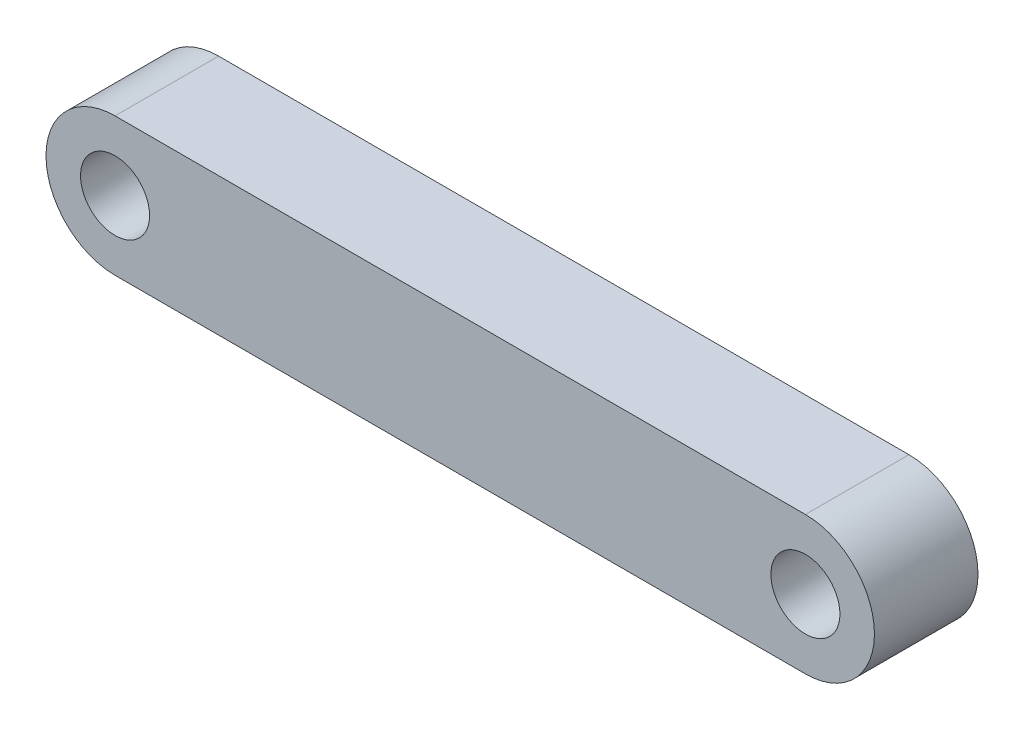
SolidWorks part; units mm, degrees
ref_plane "前视基准面" through (0, 0, 0) normal (0, 0, 1) x (1, 0, 0)
ref_plane "上视基准面" through (0, 0, 0) normal (0, 1, 0) x (1, 0, 0)
ref_plane "右视基准面" through (0, 0, 0) normal (1, 0, 0) x (0, 0, -1)
sketch "草图1" plane through (0, 0, 0) normal (0, 0, 1) x (1, 0, 0)
  line L1 (0, 0) -> (100, 0)
  line L2 (0, 0) -> (0, -20)
  line L3 (0, -20) -> (100, -20)
  line L4 (100, 0) -> (100, -20)
  circle A0 centre (0, -10) radius 10
  circle A1 centre (100, -10) radius 10
  circle A2 centre (0, -10) radius 5
  circle A3 centre (100, -10) radius 5
extrude "凸台-拉伸1" add sketch "草图1" along normal blind 15 contours A1 L1 A0 L3 | A2 L2 A0 | A2 L2 A0 | A3 L4 A1 | A3 L4 A1
ref_plane "基准面1" through (100, -20, 0) normal (0, 0, -1) x (-1, 0, 0)
